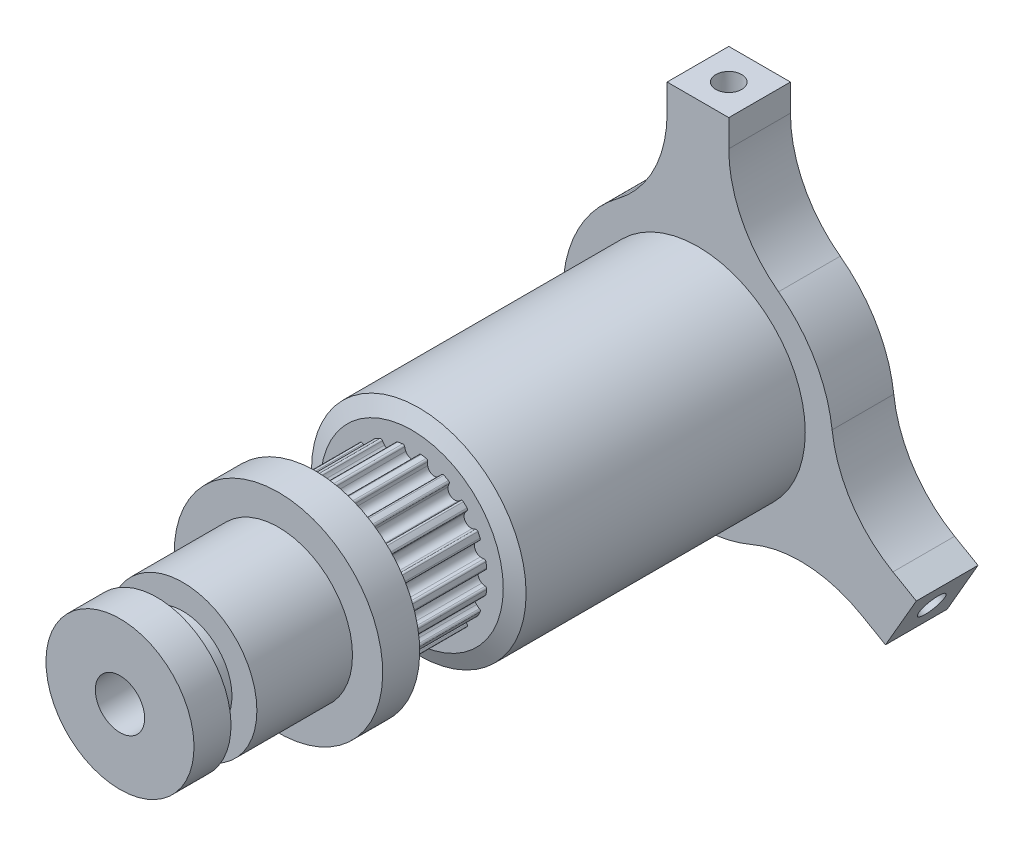
SolidWorks part; units mm, degrees
ref_plane "Front Plane" through (0, 0, 0) normal (0, 0, 1) x (1, 0, 0)
ref_plane "Top Plane" through (0, 0, 0) normal (0, 1, 0) x (1, 0, 0)
ref_plane "Right Plane" through (0, 0, 0) normal (1, 0, 0) x (0, 0, -1)
sketch "Sketch10" plane through (0, 0, 0) normal (0, 0, 1) x (1, 0, 0)
  circle A0 centre (0, 0) radius 2 construction
  dimension "D1" = 4
sketch "Sketch1" plane through (0, 0, 0) normal (0, 0, 1) x (1, 0, 0)
  line L5 (7.9825, -7.4955) -> (15.2045, -11.6651)
  line L6 (10.4825, -3.1653) -> (17.7045, -7.3349)
  line L7 (15.2045, -11.6651) -> (17.7045, -7.3349)
  line L9 (-10.4825, -3.1653) -> (-17.7045, -7.3349)
  line L10 (-7.9825, -7.4955) -> (-15.2045, -11.6651)
  line L11 (-17.7045, -7.3349) -> (-15.2045, -11.6651)
  line L13 (-2.5, 10.6608) -> (-2.5, 19)
  line L14 (2.5, 10.6608) -> (2.5, 19)
  line L15 (-2.5, 19) -> (2.5, 19)
  line L16 (-10.4825, -3.1653) -> (-2.5, 10.6608) construction
  line L17 (2.5, 10.6608) -> (10.4825, -3.1653) construction
  line L18 (-7.9825, -7.4955) -> (7.9825, -7.4955) construction
  line L19 (2.5, 19) -> (17.7045, -7.3349) construction
  line L20 (15.2045, -11.6651) -> (-15.2045, -11.6651) construction
  line L21 (-17.7045, -7.3349) -> (-2.5, 19) construction
  arc A0 (10.4825, -3.1653) -> (2.5, 10.6608) centre (0, 0) ccw
  arc A1 (-2.5, 10.6608) -> (-10.4825, -3.1653) centre (0, 0) ccw
  arc A2 (-7.9825, -7.4955) -> (7.9825, -7.4955) centre (0, 0) ccw
  dimension "D1" = 21.9
  dimension "D2" = 5
  dimension "D3" = 19
extrude "Boss-Extrude1" add sketch "Sketch1" along normal blind 5
sketch "main_revolve_sketch" plane through (0, 0, 0) normal (1, 0, 0) x (0, 0, -1)
  line L0 (-5, 0) -> (-5, 8.7)
  line L1 (-5, 8.7) -> (-27.63, 8.7)
  line L2 (-27.63, 8.7) -> (-28.1868, 7.404)
  line L3 (-28.1868, 7.404) -> (-28.1868, 6.1085)
  line L4 (-28.1868, 6.1085) -> (-35.5568, 6.1085)
  line L5 (-35.5568, 6.1085) -> (-35.5568, 7.404)
  line L6 (-35.5568, 7.404) -> (-36.0063, 8.45)
  line L7 (-36.0063, 8.45) -> (-39.0063, 8.45)
  line L8 (-5, 0) -> (-39.0063, 0) construction
  line L9 (-39.0063, 8.45) -> (-39.0063, 0)
  line L10 (-35.5568, 7.404) -> (-36.1137, 8.7) construction
  line L11 (-31.8718, 6.1085) -> (-31.8718, 0) construction
  line L12 (-5, 10.6608) -> (-5, -3.1653) construction
  line L13 (-5, 0) -> (-39.0063, 0)
  line L14 (-36.1137, 8.7) -> (-27.63, 8.7) construction
  line L15 (-31.8718, 8.7) -> (-31.8718, 6.1085) construction
  dimension "D1" = 17.4
  dimension "D2" = 7.37
  dimension "D3" = 8.38
  dimension "D4" = 12.217
  dimension "D5" = 14.808
  dimension "length_difference" = 22.63
  dimension "D7" = 3
  dimension "D8" = 0.25
revolve "main_revolve" add sketch "main_revolve_sketch" angle 360 about L13
sketch "Sketch11" plane through (0, 0, 39.0063) normal (0, 0, 1) x (1, 0, 0)
  circle A2 centre (0, 0) radius 6
  circle A3 centre (0, 0) radius 6
  dimension "D1" = 4
extrude "Boss-Extrude3" add sketch "Sketch11" along normal blind 7.75
sketch "Sketch13" plane through (0, 0, 0) normal (1, 0, 0) x (0, 0, -1)
  line L0 (-46.7563, 0) -> (-46.7563, 3.9775)
  line L1 (-46.7563, 6) -> (-46.7563, -6) construction
  line L2 (-46.7563, 3.9775) -> (-48.8563, 3.9775)
  line L3 (-48.8563, 3.9775) -> (-48.8563, 6)
  line L4 (-48.8563, 6) -> (-51.8563, 6)
  line L5 (-51.8563, 6) -> (-51.8563, 0)
  line L6 (-51.8563, 0) -> (-46.7563, 0) construction
  line L7 (-39.0063, 6) -> (-46.7563, 6) construction
  line L8 (-46.7563, 0) -> (-51.8563, 0)
  dimension "D1" = 3
  dimension "D2" = 2.1
  dimension "D3" = 7.955
revolve "Revolve2" add sketch "Sketch13" angle 360 about L6
sketch "Sketch2" plane through (0, 19, 0) normal (0, 1, 0) x (1, 0, 0)
  line L0 (0, 0) -> (0, -2.5) construction
  line L1 (0, -2.5) -> (2.5, -2.5) construction
  line L2 (2.5, -5) -> (2.5, 0) construction
  circle A0 centre (0, -2.5) radius 1.05
  dimension "D1" = 2.1
extrude "Cut-Extrude1" cut sketch "Sketch2" against normal blind 10
pattern_circular "CirPattern2" count 3 over 360 about axis through (0, 0, 0) along (0, 0, 1) of "Cut-Extrude1"
draft "Draft4" type of draft neutral plane draft angle 1 faces to draft 1 face at (0, 9, 3.55) neutral plane through (-2.5, 19, 5) neutral plane normal (0, 1, 0) parameters "D1"=1
draft "Draft5" type of draft neutral plane draft angle 1 faces to draft 1 face at (-7.7942, -4.5, 3.55) neutral plane through (-17.7045, -7.3349, 5) neutral plane normal (-0.866, -0.5, 0) parameters "D1"=1
draft "Draft6" type of draft neutral plane draft angle 1 faces to draft 1 face at (7.7942, -4.5, 3.55) neutral plane through (15.2045, -11.6651, 5) neutral plane normal (0.866, -0.5, 0) parameters "D1"=1
sketch "Sketch3" plane through (0, 0, 0) normal (0, 0, -1) x (-1, 0, 0)
  circle A0 centre (0, 0) radius 2
  circle A1 centre (0, 0) radius 2 construction
extrude "Cut-Extrude2" cut sketch "Sketch3" against normal through all
sketch "Sketch7" plane through (0, 0, 28.1868) normal (0, 0, 1) x (1, 0, 0)
  line B0 (0, 0) -> (0, 5.3585) construction
  line B1 (-1.8963, 5.8067) -> (-2.841, 8.6995)
  line B2 (-2.841, 8.6995) -> (2.841, 8.6995)
  line B3 (2.841, 8.6995) -> (1.8963, 5.8067)
  arc B4 (-0.4989, 5.6703) -> (0.4989, 5.6703) centre (0, 5.9135) ccw
  arc B5 (-0.4989, 5.6703) -> (-0.5855, 5.9387) centre (0.4, 6.1085) cw
  arc B6 (-1.8963, 5.8067) -> (-0.7518, 6.0621) centre (0, 0) cw
  arc B7 (-0.5855, 5.9387) -> (-0.7518, 6.0621) centre (-0.7333, 5.9132) ccw
  arc B8 (1.8963, 5.8067) -> (0.7518, 6.0621) centre (0, 0) ccw
  arc B9 (0.5855, 5.9387) -> (0.7518, 6.0621) centre (0.7333, 5.9132) cw
  arc B10 (0.4989, 5.6703) -> (0.5855, 5.9387) centre (-0.4, 6.1085) ccw
sketch_block_instance "Block-Gt Timing Belt Pulley Groove-1"
sketch_block "Block-Gt Timing Belt Pulley Groove" parameters "D1"=12.725, "D2"=17.399, "D6"=0.555, "D7"=1, "D9"=0.15, "D3"=9.6972, "D4"=4.8486, "D5"=2, "D8"=0.254, "D10"=0.4, "D11"=0.75
extrude "Cut-Extrude3" cut sketch "Sketch7" along normal up to surface (7.37 mm away) up to face at (0, 7.404, 35.5568)
pattern_circular "CirPattern4" count 20 over 360 about axis through (0, 0, 0) along (0, 0, 1) of "Cut-Extrude3"
fillet "Fillet1" radius 10 6 edges at (2.5, 10.6608, 2.5) (10.4825, -3.1653, 2.5) (7.9825, -7.4955, 2.5) (-7.9825, -7.4955, 2.5) (-10.4825, -3.1653, 2.5) (-2.5, 10.6608, 2.5)
ref_plane "Plane1" through (0, 0, 31.8718) normal (0, 0, 1) x (1, 0, 0)
